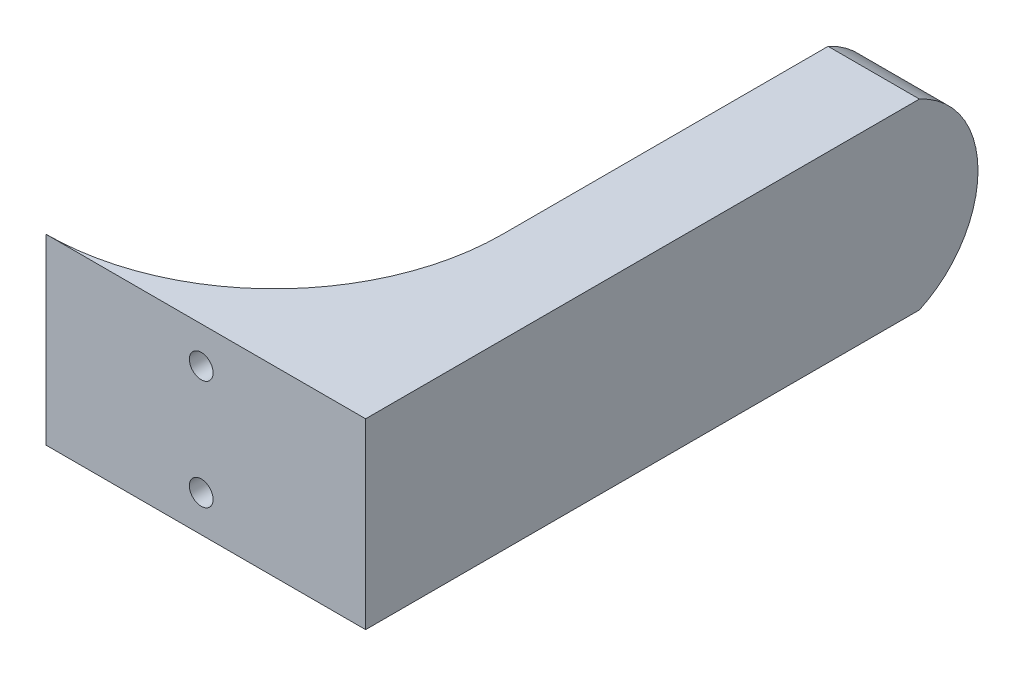
SolidWorks part; units mm, degrees
ref_plane "Front Plane" through (0, 0, 0) normal (0, 0, 1) x (1, 0, 0)
ref_plane "Top Plane" through (0, 0, 0) normal (0, 1, 0) x (1, 0, 0)
ref_plane "Right Plane" through (0, 0, 0) normal (1, 0, 0) x (0, 0, -1)
sketch "Sketch1" plane through (0, 0, 0) normal (0, 1, 0) x (1, 0, 0)
  line L0 (0, 0) -> (0, -59.69)
  line L1 (31.75, -91.44) -> (69.85, -91.44)
  line L2 (101.6, -59.69) -> (101.6, 0)
  line L3 (101.6, 0) -> (114.3, 0)
  line L4 (114.3, 0) -> (114.3, -99.06)
  line L5 (114.3, -99.06) -> (-7.62, -99.06)
  line L6 (-7.62, -99.06) -> (-7.62, 0)
  line L7 (-7.62, 0) -> (0, 0)
  arc A0 (69.85, -91.44) -> (101.6, -59.69) centre (69.85, -59.69) ccw
  arc A1 (0, -59.69) -> (31.75, -91.44) centre (31.75, -59.69) ccw
  point P11 (101.6, -91.44)
  point P14 (0, -91.44)
  dimension "D6" = 31.75
  dimension "D1" = 101.6
  dimension "D2" = 7.62
  dimension "D3" = 12.7
  dimension "D4" = 7.62
  dimension "D5" = 91.44
extrude "Boss-Extrude1" add sketch "Sketch1" along normal blind 25.4
sketch "Sketch2" plane through (0, 0, 0) normal (1, 0, 0) x (0, 0, -1)
  line L0 (0, 25.4) -> (0, 0) construction
  line L2 (0, 25.4) -> (0, 0) construction
  circle A2 centre (-15.24, 12.7) radius 1.5875
  circle A3 centre (-45.72, 12.7) radius 1.5875
  circle A4 centre (-30.48, 12.7) radius 3.302
  point P4 (0, 12.7)
  dimension "D1" = 30.48
  dimension "D3" = 3.175
  dimension "D4" = 6.604
  dimension "D8" = 3.175
  dimension "D2" = 15.24
  dimension "D5" = 15.24
sketch "Sketch4" plane through (101.6, 0, 0) normal (-1, 0, 0) x (0, 0, 1)
  line L0 (0, 25.4) -> (0, 0) construction
  circle A0 centre (30.48, 12.7) radius 3.302
  point P4 (0, 12.7)
  dimension "D1" = 30.48
  dimension "D2" = 6.604
extrude "Cut-Extrude2" cut sketch "Sketch4" against normal blind 7.62 contours A0
extrude "Cut-Extrude3" cut sketch "Sketch2" against normal blind 7.62
sketch "Sketch6" plane through (0, 0, 99.06) normal (0, 0, 1) x (1, 0, 0)
  line L0 (-7.62, 25.4) -> (114.3, 25.4) construction
  line L1 (-7.62, 25.4) -> (114.3, 25.4)
  line L2 (-7.62, 25.4) -> (-7.62, 38.1)
  line L3 (-7.62, 38.1) -> (114.3, 38.1)
  line L4 (114.3, 25.4) -> (114.3, 38.1)
  line L5 (-7.62, 0) -> (114.3, 0) construction
  line L6 (-7.62, 0) -> (114.3, 0)
  line L7 (-7.62, 0) -> (-7.62, -12.7)
  line L8 (-7.62, -12.7) -> (114.3, -12.7)
  line L9 (114.3, 0) -> (114.3, -12.7)
  line L10 (-7.62, 25.4) -> (-7.62, 0) construction
  line L11 (114.3, 25.4) -> (114.3, 0) construction
  point P13 (53.34, 25.4)
  point P14 (53.34, 0)
  dimension "D1" = 50.8
extrude "Boss-Extrude2" add sketch "Sketch6" against normal up to surface (7.62 mm away) up to face at (50.8, 12.7, 91.44)
sketch "Sketch7" plane through (0, 0, 99.06) normal (0, 0, 1) x (1, 0, 0)
  line L0 (-7.62, 38.1) -> (-7.62, -12.7) construction
  line L1 (12.2844, 29.21) -> (9.9014, 33.3375)
  line L2 (9.9014, 33.3375) -> (5.1354, 33.3375)
  line L3 (5.1354, 33.3375) -> (2.7524, 29.21)
  line L4 (2.7524, 29.21) -> (5.1354, 25.0825)
  line L5 (5.1354, 25.0825) -> (9.9014, 25.0825)
  line L6 (9.9014, 25.0825) -> (12.2844, 29.21)
  line L7 (103.7244, -3.81) -> (101.3414, 0.3175)
  line L8 (101.3414, 0.3175) -> (96.5754, 0.3175)
  line L9 (96.5754, 0.3175) -> (94.1924, -3.81)
  line L10 (94.1924, -3.81) -> (96.5754, -7.9375)
  line L11 (96.5754, -7.9375) -> (101.3414, -7.9375)
  line L12 (101.3414, -7.9375) -> (103.7244, -3.81)
  line L13 (114.3, 25.4) -> (114.3, 38.1) construction
  circle A2 centre (7.5184, 29.21) radius 4.1275 construction
  circle A3 centre (98.9584, -3.81) radius 4.1275 construction
  point P21 (-7.62, 12.7)
  dimension "D1" = 8.255
  dimension "D2" = 8.255
  dimension "D3" = 16.51
  dimension "D4" = 33.02
  dimension "D5" = 91.44
  dimension "D6" = 15.3416
extrude "Cut-Extrude4" cut sketch "Sketch7" against normal blind 3.81
sketch "Sketch8" plane through (0, 0, 99.06) normal (0, 0, 1) x (1, 0, 0)
  circle A0 centre (7.5184, 29.21) radius 4.1275
  circle A1 centre (98.9584, -3.81) radius 4.1275
  dimension "D1" = 8.255
  dimension "D2" = 8.255
sketch "Sketch10" plane through (-7.62, 0, 0) normal (-1, 0, 0) x (0, 0, 1)
  circle A1 centre (15.24, 12.7) radius 2.921
  circle A2 centre (45.72, 12.7) radius 2.921
  dimension "D1" = 5.842
  dimension "D2" = 5.842
extrude "Cut-Extrude5" cut sketch "Sketch10" against normal blind 3.048
sketch "Sketch11" plane through (0, 0, 95.25) normal (0, 0, 1) x (1, 0, 0)
  circle A0 centre (7.5184, 29.21) radius 1.5875
  circle A1 centre (98.9584, -3.81) radius 1.5875
  dimension "D1" = 3.175
  dimension "D2" = 3.175
extrude "Cut-Extrude6" cut sketch "Sketch11" against normal through all
sketch "Sketch12" plane through (0, 0, 99.06) normal (0, 0, 1) x (1, 0, 0)
  line L0 (-7.62, -12.7) -> (114.3, -12.7) construction
  line L1 (67.2846, 22.86) -> (58.3946, 22.86)
  line L2 (67.2846, 22.86) -> (67.2846, 2.54)
  line L3 (67.2846, 2.54) -> (58.3946, 2.54)
  line L4 (58.3946, 22.86) -> (58.3946, 2.54)
  line L6 (-7.62, 25.4) -> (-7.62, 38.1) construction
  dimension "D1" = 15.24
  dimension "D2" = 66.0146
  dimension "D3" = 8.89
  dimension "D4" = 20.32
extrude "Cut-Extrude7" cut sketch "Sketch12" against normal up to next
sketch "Sketch14" plane through (-7.62, 0, 0) normal (-1, 0, 0) x (0, 0, 1)
  line L0 (0, 25.4) -> (91.44, 25.4) construction
  line L1 (0, 0) -> (91.44, 0) construction
  line L2 (14.4264, 25.4) -> (0, 25.4)
  line L3 (0, 25.4) -> (0, 0)
  line L4 (0, 0) -> (14.4264, 0)
  arc A0 (14.4264, 25.4) -> (14.4264, 0) centre (20.2462, 12.7) ccw
  dimension "D1" = 13.97
extrude "Cut-Extrude8" cut sketch "Sketch14" against normal through all both and the other way through all
sketch "Sketch15" plane through (0, 0, 91.44) normal (0, 0, -1) x (-1, 0, 0)
  line L0 (-114.3, 38.1) -> (-114.3, 25.4) construction
  line L1 (-67.2846, 22.86) -> (-67.2846, 2.54) construction
  line L3 (-88.1404, 20.32) -> (-89.7902, 23.1775)
  line L4 (-89.7902, 23.1775) -> (-93.0898, 23.1775)
  line L5 (-93.0898, 23.1775) -> (-94.7396, 20.32)
  line L6 (-94.7396, 20.32) -> (-93.0898, 17.4625)
  line L7 (-93.0898, 17.4625) -> (-89.7902, 17.4625)
  line L8 (-89.7902, 17.4625) -> (-88.1404, 20.32)
  line L9 (-88.1404, 5.08) -> (-89.7902, 7.9375)
  line L10 (-89.7902, 7.9375) -> (-93.0898, 7.9375)
  line L11 (-93.0898, 7.9375) -> (-94.7396, 5.08)
  line L12 (-94.7396, 5.08) -> (-93.0898, 2.2225)
  line L13 (-93.0898, 2.2225) -> (-89.7902, 2.2225)
  line L14 (-89.7902, 2.2225) -> (-88.1404, 5.08)
  circle A2 centre (-91.44, 20.32) radius 2.8575 construction
  circle A3 centre (-91.44, 5.08) radius 2.8575 construction
  point P8 (-67.2846, 12.7)
  dimension "D6" = 5.715
  dimension "D7" = 5.715
  dimension "D3" = 22.86
  dimension "D4" = 15.24
  dimension "D5" = 7.62
extrude "Cut-Extrude9" cut sketch "Sketch15" along normal through all
sketch "Sketch16" plane through (0, 38.1, 0) normal (0, 1, 0) x (1, 0, 0)
  line L1 (114.3, -91.44) -> (-7.62, -91.44)
  line L2 (114.3, -91.44) -> (114.3, -99.06)
  line L3 (114.3, -99.06) -> (-7.62, -99.06)
  line L4 (-7.62, -91.44) -> (-7.62, -99.06)
  line L5 (-7.62, -6.2762) -> (37.3212, -6.2762)
  line L6 (-7.62, -6.2762) -> (-7.62, -91.44)
  line L7 (-7.62, -91.44) -> (37.3212, -91.44)
  line L8 (37.3212, -6.2762) -> (37.3212, -91.44)
extrude "Cut-Extrude10" cut sketch "Sketch16" against normal through all contours L8 L5 L6 L1
sketch "Sketch17" plane through (0, 25.4, 0) normal (0, 1, 0) x (1, 0, 0)
  line L0 (114.3, -91.44) -> (69.85, -91.44) construction
  line L1 (75.9994, -91.44) -> (65.5253, -91.44)
  line L2 (75.9994, -91.44) -> (75.9994, -88.4966)
  line L3 (75.9994, -88.4966) -> (65.5253, -88.4966)
  line L4 (65.5253, -91.44) -> (65.5253, -88.4966)
sketch "Sketch18" plane through (0, 0, 91.44) normal (0, 0, 1) x (1, 0, 0)
  circle A0 centre (91.2267, 20.5219) radius 4.468
  circle A1 centre (91.7577, 5.0161) radius 4.1102
extrude "Boss-Extrude3" add sketch "Sketch18" against normal blind 2.54
sketch "Sketch19" plane through (0, 0, 91.44) normal (0, 0, 1) x (1, 0, 0)
  line L0 (114.3, 0) -> (114.3, 25.4) construction
  line L1 (114.3, 25.4) -> (69.85, 25.4) construction
  circle A0 centre (91.44, 20.32) radius 1.651
  circle A1 centre (91.44, 5.08) radius 1.651
  point P4 (0, 0)
  dimension "D1" = 3.302
  dimension "D2" = 3.302
  dimension "D3" = 15.24
  dimension "D4" = 22.86
  dimension "D5" = 5.08
extrude "Cut-Extrude11" cut sketch "Sketch19" against normal blind 2.54
